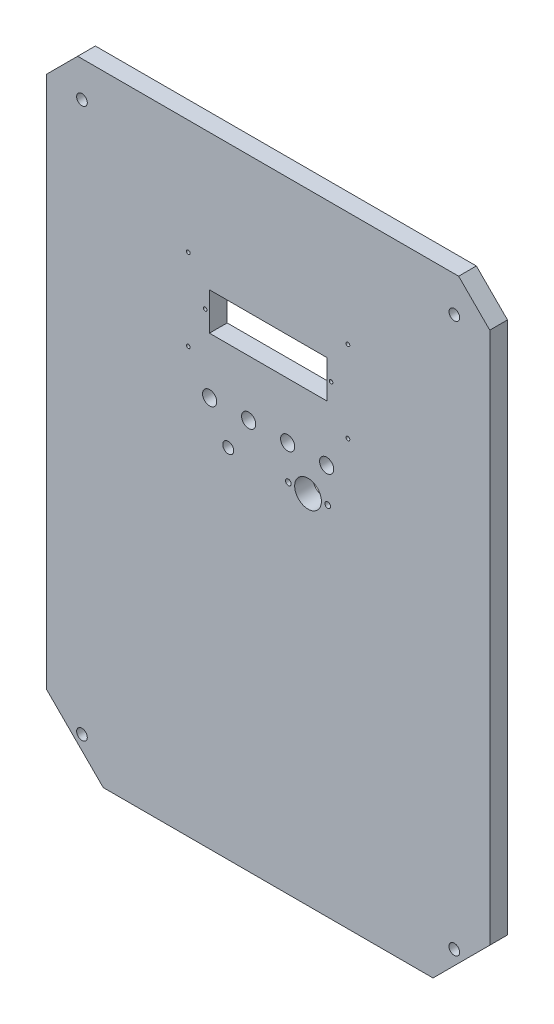
SolidWorks part; units mm, degrees
ref_plane "Plan de face" through (0, 0, 0) normal (0, 0, 1) x (1, 0, 0)
ref_plane "Plan de dessus" through (0, 0, 0) normal (0, 1, 0) x (1, 0, 0)
ref_plane "Plan de droite" through (0, 0, 0) normal (1, 0, 0) x (0, 0, -1)
sketch "Esquisse1" plane through (0, 0, 0) normal (0, 0, 1) x (1, 0, 0)
  line L0 (907.6014, 522.6101) -> (939.6014, 554.6101)
  line L1 (721.6014, 522.6101) -> (907.6014, 522.6101)
  line L2 (689.6014, 554.6101) -> (721.6014, 522.6101)
  line L3 (689.6014, 855.0427) -> (689.6014, 554.6101)
  line L4 (707.1688, 872.6101) -> (689.6014, 855.0427)
  line L5 (922.034, 872.6101) -> (707.1688, 872.6101)
  line L6 (939.6014, 855.0427) -> (922.034, 872.6101)
  line L7 (939.6014, 554.6101) -> (939.6014, 855.0427)
  line L8 (814.6014, 803.1101) -> (814.6014, 767.1101) construction
  line L9 (854.6014, 803.1101) -> (774.6014, 803.1101) construction
  line L10 (854.6014, 803.1101) -> (854.6014, 767.1101) construction
  line L11 (854.6014, 767.1101) -> (774.6014, 767.1101) construction
  line L12 (774.6014, 803.1101) -> (774.6014, 767.1101) construction
  line L13 (774.6014, 785.1101) -> (854.6014, 785.1101) construction
  line L14 (814.6014, 872.6101) -> (814.6014, 522.6101) construction
  line L15 (847.7014, 795.7101) -> (781.5014, 795.7101)
  line L16 (847.7014, 795.7101) -> (847.7014, 774.5101)
  line L17 (847.7014, 774.5101) -> (781.5014, 774.5101)
  line L18 (781.5014, 795.7101) -> (781.5014, 774.5101)
  line L19 (847.7014, 795.7101) -> (781.5014, 774.5101) construction
  line L20 (847.7014, 774.5101) -> (781.5014, 795.7101) construction
  line L21 (689.6014, 704.8264) -> (939.6014, 704.8264) construction
  line L22 (848.2014, 723.9208) -> (826.0014, 723.9208) construction
  line L23 (939.6014, 743.0154) -> (689.6014, 743.0154) construction
  line L24 (939.6014, 723.9208) -> (689.6014, 723.9208) construction
  circle A0 centre (709.6014, 542.6101) radius 3
  circle A1 centre (709.6014, 852.6101) radius 3
  circle A2 centre (919.6014, 852.6101) radius 3
  circle A3 centre (919.6014, 542.6101) radius 3
  circle A4 centre (859.6014, 808.1101) radius 1.05
  circle A5 centre (769.6014, 808.1101) radius 1.05
  circle A6 centre (769.6014, 762.1101) radius 1.05
  circle A7 centre (859.6014, 762.1101) radius 1.05
  circle A8 centre (850.1014, 785.1101) radius 1
  circle A9 centre (779.1014, 785.1101) radius 1
  circle A10 centre (837.1014, 723.9208) radius 7.55
  circle A11 centre (847.6014, 743.0154) radius 4
  circle A12 centre (837.1014, 723.9208) radius 11.1 construction
  circle A13 centre (848.2014, 723.9208) radius 1.6
  circle A14 centre (826.0014, 723.9208) radius 1.6
  circle A15 centre (825.6014, 743.0154) radius 4
  circle A16 centre (803.6014, 743.0154) radius 4
  circle A17 centre (781.6014, 743.0154) radius 4
  circle A18 centre (792.1014, 723.9208) radius 3.1
  point P32 (814.6014, 785.1101)
  dimension "D4" = 2.1
  dimension "D9" = 2
  dimension "D17" = 20
  dimension "D18" = 20
  dimension "D19" = 15.1
  dimension "D20" = 8
  dimension "D21" = 22.2
  dimension "D22" = 3.2
  dimension "D23" = 3.2
  dimension "D27" = 0
  dimension "D1" = 310
  dimension "D2" = 80
  dimension "D3" = 36
  dimension "D5" = 5
  dimension "D6" = 5
  dimension "D7" = 66.2
  dimension "D8" = 21.2
  dimension "D10" = 35.5
  dimension "D11" = 20
  dimension "D12" = 20
  dimension "D13" = 20
  dimension "D14" = 20
  dimension "D15" = 20
  dimension "D16" = 20
  dimension "D24" = 87.5
  dimension "D25" = 250
  dimension "D26" = 125
  dimension "D28" = 19.0947
  dimension "D29" = 19.0947
  dimension "D30" = 19.0944
  dimension "D31" = 0
  dimension "D32" = 0
  dimension "D33" = 0
  dimension "D34" = 0
  dimension "D35" = 22.5
  dimension "D36" = 0
  dimension "D37" = 22.5
  dimension "D38" = 11
  dimension "D39" = 11
  dimension "D40" = 22
  dimension "D41" = 22
extrude "Boss.-Extru.1" add sketch "Esquisse1" along normal blind 10
